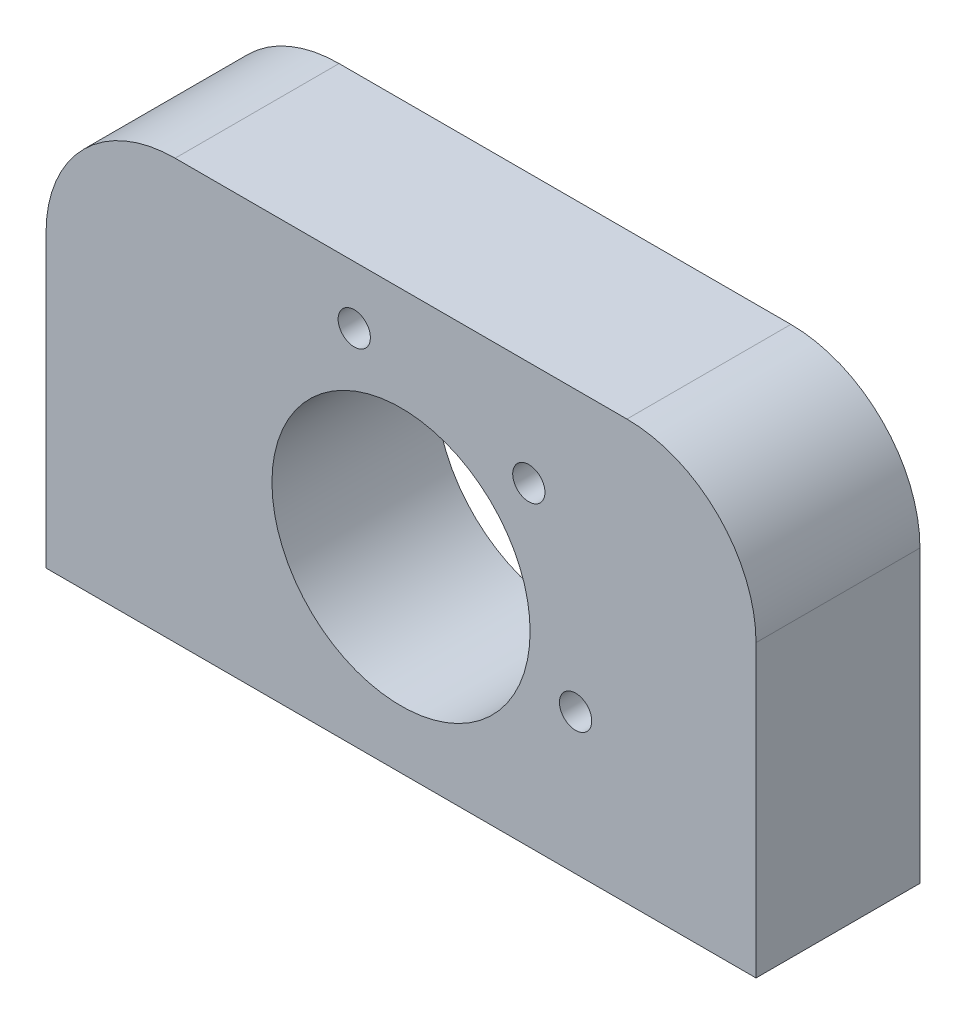
SolidWorks part; units mm, degrees
material "6061 Alloy"
ref_plane "Front Plane" through (0, 0, 0) normal (0, 0, 1) x (1, 0, 0)
ref_plane "Top Plane" through (0, 0, 0) normal (0, 1, 0) x (1, 0, 0)
ref_plane "Right Plane" through (0, 0, 0) normal (1, 0, 0) x (0, 0, -1)
sketch "Sketch2" plane through (0, 0, 0) normal (0, 0, 1) x (1, 0, 0)
  line L0 (0, 0) -> (0, 14.5) construction
  line L1 (27.5, 0) -> (-27.5, 0)
  line L2 (-27.5, 0) -> (-27.5, 22.5)
  line L3 (-17.5, 32.5) -> (17.5, 32.5)
  line L4 (27.5, 0) -> (27.5, 22.5)
  circle A0 centre (0, 14.5) radius 10
  circle A1 centre (0, 14.5) radius 19 construction
  circle A2 centre (0, 14.5) radius 14 construction
  arc A3 (-27.5, 22.5) -> (-17.5, 32.5) centre (-17.5, 22.5) cw
  arc A4 (27.5, 22.5) -> (17.5, 32.5) centre (17.5, 22.5) ccw
  point P11 (-24.8843, 34.9021)
  point P16 (0, 32.5)
  dimension "D2" = 20
  dimension "D3" = 38
  dimension "D4" = 28
  dimension "D8" = 10
  dimension "D9" = 22.5
  dimension "D1" = 14.5
  dimension "D5" = 27.5
  dimension "D6" = 35
  dimension "D7" = 25
extrude "Boss-Extrude1" add sketch "Sketch2" along normal blind 12.7
sketch "Sketch3" plane through (0, 0, 0) normal (0, 0, -1) x (-1, 0, 0)
  line L0 (0, 0) -> (0, 14.5) construction
  line L1 (0, 14.453) -> (0, 14.5) construction
  line L2 (0, 14.5) -> (0, 32.5) construction
  line L3 (-17.5, 32.5) -> (17.5, 32.5) construction
  line L4 (0, 14.5) -> (3.6235, 28.023) construction
  line L5 (0, 14.5) -> (-9.8995, 24.3995) construction
  line L6 (0, 14.5) -> (-13.523, 10.8765)
  circle A0 centre (0, 14.5) radius 14
  point P10 (3.6235, 28.023)
  point P13 (-9.8995, 24.3995)
  point P14 (-13.523, 10.8765)
  dimension "D2" = 28
  dimension "D1" = 14.5
  dimension "D3" = 15
  dimension "D4" = 45
  dimension "D5" = 120
hole_wizard "Tap Drill for M3x0.5 Tap1" positions "3DSketch1" profile "Sketch4" hole size "M3x0.5" standard "ANSI Metric"
sketch3d "3DSketch1"
  point P0 (13.523, 10.8765, 0)
  point P3 (9.8995, 24.3995, 0)
  point P6 (-3.6235, 28.023, 0)
sketch "Sketch4" plane through (13.523, 10.8765, 0) normal (1, 0, 0) x (0, 1, 0)
  line L0 (0, 0) -> (0, 25.7511)
  line L1 (0, 25.7511) -> (1.25, 25)
  line L2 (1.25, 25) -> (1.25, 0)
  line L5 (1.25, 0) -> (0, 0)
  line L10 (0, 25.7511) -> (-1.25, 25) construction
  line L11 (0, -6.35) -> (0, 107.95) construction
  dimension "Hole Dia." = 2.5
  dimension "Hole Depth" = 25
  dimension "Drill Angle" = 118
sketch "Sketch5" plane through (0, 0, 0) normal (0, -1, 0) x (-1, 0, 0)
  line L0 (0, 0) -> (0, -12.7) construction
  line L1 (27.5, -12.7) -> (-27.5, -12.7) construction
  line L2 (-27.5, -6.35) -> (27.5, -6.35) construction
  line L3 (-27.5, -12.7) -> (-27.5, 0) construction
  line L4 (27.5, -12.7) -> (27.5, 0) construction
  point P13 (-22.25, -6.35)
  point P14 (22.25, -6.35)
  dimension "D1" = 6.35
  dimension "D2" = 22.25
hole_wizard "M4x0.7 Tapped Hole1" positions "3DSketch2" profile "Sketch6" tap size "M4x0.7" standard "ANSI Metric"
sketch3d "3DSketch2"
  point P0 (22.25, 0, 6.35)
  point P3 (-22.25, 0, 6.35)
sketch "Sketch6" plane through (22.25, 0, 6.35) normal (1, 0, 0) x (0, 0, -1)
  line L0 (0, 0) -> (0, 14.9914)
  line L1 (0, 14.9914) -> (1.65, 14)
  line L2 (1.65, 14) -> (1.65, 0)
  line L5 (1.65, 0) -> (0, 0)
  line L10 (0, 14.9914) -> (-1.65, 14) construction
  line L11 (0, -6.35) -> (0, 107.95) construction
  dimension "Tap Drill Dia." = 3.3
  dimension "Tap Drill Depth" = 14
  dimension "Drill Angle" = 118
cosmetic thread "Hole Thread1" parameters "D1"=8, "D2"=4
cosmetic thread "Hole Thread2" parameters "D1"=8, "D2"=4
